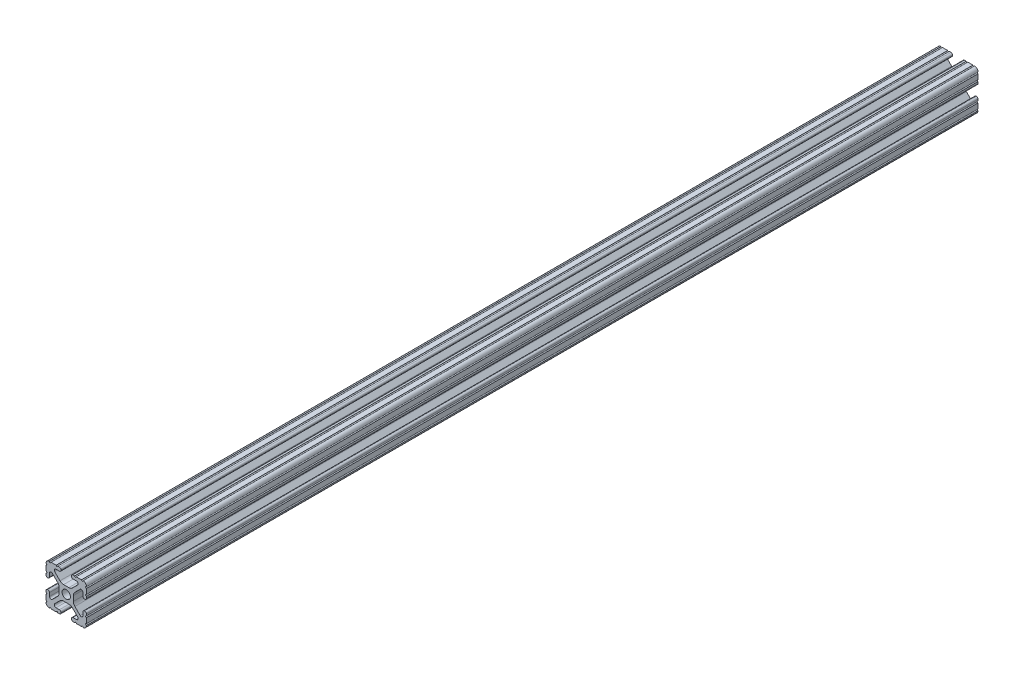
SolidWorks part; units mm, degrees
material "6061-T6 (SS)"
ref_plane "Front Plane" through (0, 0, 0) normal (0, 0, 1) x (1, 0, 0)
ref_plane "Top Plane" through (0, 0, 0) normal (0, 1, 0) x (1, 0, 0)
ref_plane "Right Plane" through (0, 0, 0) normal (1, 0, 0) x (0, 0, -1)
sketch "Sketch1" plane through (0, 0, 0) normal (0, 1, 0) x (1, 0, 0)
  line L0 (0, 0) -> (0, 560)
  dimension "D1" = 560
other "Imperial al extrusion 1010 PROFILE(1)"
ref_plane "Plane1" through (0, 0, 0) normal (0, 0, -1) x (-1, 0, 0)
sketch "Sketch16" plane through (0, 0, 0) normal (0, 0, -1) x (-1, 0, 0)
  line L1 (12.7, 12.7) -> (-12.7, 12.7) construction
  line L2 (12.7, 12.7) -> (12.7, -12.7) construction
  line L3 (12.7, -12.7) -> (-12.7, -12.7) construction
  line L4 (-12.7, 12.7) -> (-12.7, -12.7) construction
  line L5 (12.7, 12.7) -> (-12.7, -12.7) construction
  line L6 (12.7, -12.7) -> (-12.7, 12.7) construction
  line L88 (-1.7093, -4.4958) -> (1.7093, -4.4958)
  line L89 (3.9523, -5.4237) -> (7.1797, -8.6452)
  line L90 (6.4164, -10.4902) -> (4.2875, -10.4902)
  line L91 (3.2385, -11.5392) -> (3.2385, -11.651)
  line L92 (4.2875, -12.7) -> (5.3171, -12.7)
  line L93 (6.3331, -12.7) -> (9.5504, -12.7)
  line L94 (12.7, -9.5504) -> (12.7, -6.3331)
  line L95 (12.7, -5.3171) -> (12.7, -4.2875)
  line L96 (11.651, -3.2385) -> (11.5392, -3.2385)
  line L97 (10.4902, -4.2875) -> (10.4902, -6.4021)
  line L98 (8.737, -7.1292) -> (5.4405, -3.8388)
  line L99 (4.5085, -1.5917) -> (4.5085, 1.5917)
  line L100 (5.4405, 3.8388) -> (8.737, 7.1292)
  line L101 (10.4902, 6.4021) -> (10.4902, 4.2875)
  line L102 (11.5392, 3.2385) -> (11.651, 3.2385)
  line L103 (12.7, 4.2875) -> (12.7, 5.3171)
  line L104 (12.7, 6.3331) -> (12.7, 9.5504)
  line L105 (9.5504, 12.7) -> (6.3331, 12.7)
  line L106 (5.3171, 12.7) -> (4.2875, 12.7)
  line L107 (3.2384, 11.651) -> (3.2384, 11.5392)
  line L108 (4.2875, 10.4902) -> (6.4768, 10.4902)
  line L109 (7.2072, 8.7245) -> (3.9003, 5.4237)
  line L110 (1.6573, 4.4958) -> (-1.6573, 4.4958)
  line L111 (-3.9003, 5.4237) -> (-7.2072, 8.7245)
  line L112 (-6.4768, 10.4902) -> (-4.2875, 10.4902)
  line L113 (-3.2384, 11.5392) -> (-3.2384, 11.651)
  line L114 (-4.2875, 12.7) -> (-5.3171, 12.7)
  line L115 (-6.3331, 12.7) -> (-9.5504, 12.7)
  line L116 (-12.7, 9.5504) -> (-12.7, 6.3331)
  line L117 (-12.7, 5.3171) -> (-12.7, 4.2875)
  line L118 (-11.651, 3.2385) -> (-11.5392, 3.2385)
  line L119 (-10.4902, 4.2875) -> (-10.4902, 6.4021)
  line L120 (-8.737, 7.1292) -> (-5.4405, 3.8388)
  line L121 (-4.5085, 1.5917) -> (-4.5085, -1.5917)
  line L122 (-5.4405, -3.8388) -> (-8.737, -7.1292)
  line L123 (-10.4902, -6.4021) -> (-10.4902, -4.2875)
  line L124 (-11.5392, -3.2385) -> (-11.651, -3.2385)
  line L125 (-12.7, -4.2875) -> (-12.7, -5.3171)
  line L126 (-12.7, -6.3331) -> (-12.7, -9.5504)
  line L127 (-9.5504, -12.7) -> (-6.3331, -12.7)
  line L128 (-5.3171, -12.7) -> (-4.2875, -12.7)
  line L129 (-3.2385, -11.651) -> (-3.2385, -11.5392)
  line L130 (-4.2875, -10.4902) -> (-6.4164, -10.4902)
  line L131 (-7.1797, -8.6452) -> (-3.9523, -5.4237)
  circle A1 centre (0, 0) radius 2.6035
  arc A104 (-1.7093, -4.4958) -> (-3.9523, -5.4237) centre (-1.7093, -7.6708) ccw
  arc A105 (3.9523, -5.4237) -> (1.7093, -4.4958) centre (1.7093, -7.6708) ccw
  arc A106 (6.4164, -10.4902) -> (7.1797, -8.6452) centre (6.4164, -9.4098) ccw
  arc A107 (4.2875, -10.4902) -> (3.2385, -11.5392) centre (4.2875, -11.5392) ccw
  arc A108 (3.2385, -11.651) -> (4.2875, -12.7) centre (4.2875, -11.651) ccw
  arc A109 (6.3331, -12.7) -> (5.3171, -12.7) centre (5.8251, -12.7) ccw
  arc A110 (10.5664, -12.6998) -> (9.5504, -12.7) centre (10.0584, -12.7) ccw
  arc A111 (10.5664, -12.6998) -> (12.6998, -10.5664) centre (10.5918, -10.5918) ccw
  arc A112 (12.7, -9.5504) -> (12.6998, -10.5664) centre (12.7, -10.0584) ccw
  arc A113 (12.7, -5.3171) -> (12.7, -6.3331) centre (12.7, -5.8251) ccw
  arc A114 (12.7, -4.2875) -> (11.651, -3.2385) centre (11.651, -4.2875) ccw
  arc A115 (11.5392, -3.2385) -> (10.4902, -4.2875) centre (11.5392, -4.2875) ccw
  arc A116 (8.737, -7.1292) -> (10.4902, -6.4021) centre (9.4628, -6.4021) ccw
  arc A117 (4.5085, -1.5917) -> (5.4405, -3.8388) centre (7.6835, -1.5917) ccw
  arc A118 (5.4405, 3.8388) -> (4.5085, 1.5917) centre (7.6835, 1.5917) ccw
  arc A119 (10.4902, 6.4021) -> (8.737, 7.1292) centre (9.4628, 6.4021) ccw
  arc A120 (10.4902, 4.2875) -> (11.5392, 3.2385) centre (11.5392, 4.2875) ccw
  arc A121 (11.651, 3.2385) -> (12.7, 4.2875) centre (11.651, 4.2875) ccw
  arc A122 (12.7, 6.3331) -> (12.7, 5.3171) centre (12.7, 5.8251) ccw
  arc A123 (12.6998, 10.5664) -> (12.7, 9.5504) centre (12.7, 10.0584) ccw
  arc A124 (12.6998, 10.5664) -> (10.5664, 12.6998) centre (10.5918, 10.5918) ccw
  arc A125 (9.5504, 12.7) -> (10.5664, 12.6998) centre (10.0584, 12.7) ccw
  arc A126 (5.3171, 12.7) -> (6.3331, 12.7) centre (5.8251, 12.7) ccw
  arc A127 (4.2875, 12.7) -> (3.2384, 11.651) centre (4.2875, 11.651) ccw
  arc A128 (3.2384, 11.5392) -> (4.2875, 10.4902) centre (4.2875, 11.5392) ccw
  arc A129 (7.2072, 8.7245) -> (6.4768, 10.4902) centre (6.4768, 9.4563) ccw
  arc A130 (1.6573, 4.4958) -> (3.9003, 5.4237) centre (1.6573, 7.6708) ccw
  arc A131 (-3.9003, 5.4237) -> (-1.6573, 4.4958) centre (-1.6573, 7.6708) ccw
  arc A132 (-6.4768, 10.4902) -> (-7.2072, 8.7245) centre (-6.4768, 9.4563) ccw
  arc A133 (-4.2875, 10.4902) -> (-3.2384, 11.5392) centre (-4.2875, 11.5392) ccw
  arc A134 (-3.2384, 11.651) -> (-4.2875, 12.7) centre (-4.2875, 11.651) ccw
  arc A135 (-6.3331, 12.7) -> (-5.3171, 12.7) centre (-5.8251, 12.7) ccw
  arc A136 (-10.5664, 12.6998) -> (-9.5504, 12.7) centre (-10.0584, 12.7) ccw
  arc A137 (-10.5664, 12.6998) -> (-12.6998, 10.5664) centre (-10.5918, 10.5918) ccw
  arc A138 (-12.7, 9.5504) -> (-12.6998, 10.5664) centre (-12.7, 10.0584) ccw
  arc A139 (-12.7, 5.3171) -> (-12.7, 6.3331) centre (-12.7, 5.8251) ccw
  arc A140 (-12.7, 4.2875) -> (-11.651, 3.2385) centre (-11.651, 4.2875) ccw
  arc A141 (-11.5392, 3.2385) -> (-10.4902, 4.2875) centre (-11.5392, 4.2875) ccw
  arc A142 (-8.737, 7.1292) -> (-10.4902, 6.4021) centre (-9.4628, 6.4021) ccw
  arc A143 (-4.5085, 1.5917) -> (-5.4405, 3.8388) centre (-7.6835, 1.5917) ccw
  arc A144 (-5.4405, -3.8388) -> (-4.5085, -1.5917) centre (-7.6835, -1.5917) ccw
  arc A145 (-10.4902, -6.4021) -> (-8.737, -7.1292) centre (-9.4628, -6.4021) ccw
  arc A146 (-10.4902, -4.2875) -> (-11.5392, -3.2385) centre (-11.5392, -4.2875) ccw
  arc A147 (-11.651, -3.2385) -> (-12.7, -4.2875) centre (-11.651, -4.2875) ccw
  arc A148 (-12.7, -6.3331) -> (-12.7, -5.3171) centre (-12.7, -5.8251) ccw
  arc A149 (-12.6998, -10.5664) -> (-12.7, -9.5504) centre (-12.7, -10.0584) ccw
  arc A150 (-12.6998, -10.5664) -> (-10.5664, -12.6998) centre (-10.5918, -10.5918) ccw
  arc A151 (-9.5504, -12.7) -> (-10.5664, -12.6998) centre (-10.0584, -12.7) ccw
  arc A152 (-5.3171, -12.7) -> (-6.3331, -12.7) centre (-5.8251, -12.7) ccw
  arc A153 (-4.2875, -12.7) -> (-3.2385, -11.651) centre (-4.2875, -11.651) ccw
  arc A154 (-3.2385, -11.5392) -> (-4.2875, -10.4902) centre (-4.2875, -11.5392) ccw
  arc A155 (-7.1797, -8.6452) -> (-6.4164, -10.4902) centre (-6.4164, -9.4098) ccw
  point P3 (0, 0)
  point P21 (-12.7, 0)
  point P22 (0, 12.7)
  point P25 (12.7, 0)
  point P28 (0, -12.7)
  point P30 (-12.7, -12.7)
  point P33 (12.7, -12.7)
  point P37 (12.7, 12.7)
  point P40 (-12.7, 12.7)
  point P43 (0, 0)
  dimension "D1" = 25.4
